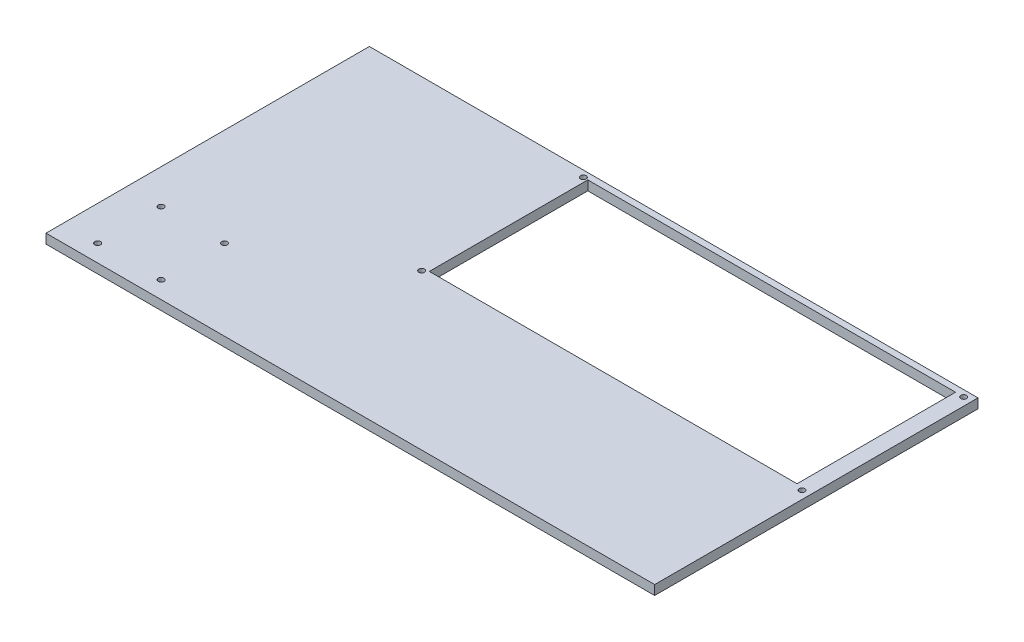
SolidWorks part; units mm, degrees
material "Balsa"
ref_plane "Front Plane" through (0, 0, 0) normal (0, 0, 1) x (1, 0, 0)
ref_plane "Top Plane" through (0, 0, 0) normal (0, 1, 0) x (1, 0, 0)
ref_plane "Right Plane" through (0, 0, 0) normal (1, 0, 0) x (0, 0, -1)
sketch "Sketch1" plane through (0, 0, 0) normal (0, 1, 0) x (1, 0, 0)
  line L1 (480, -255) -> (-480, -255)
  line L2 (480, -255) -> (480, 255)
  line L3 (480, 255) -> (-480, 255)
  line L4 (-480, -255) -> (-480, 255)
  line L5 (480, -255) -> (-480, 255) construction
  line L6 (480, 255) -> (-480, -255) construction
  point P0 (0, 0)
  dimension "D1" = 510
  dimension "D2" = 960
extrude "Boss-Extrude1" add sketch "Sketch1" along normal mid plane 15
sketch "Sketch3" plane through (0, 7.5, 0) normal (0, 1, 0) x (1, 0, 0)
  line L1 (454.5475, 245) -> (-125.4525, 245)
  line L2 (454.5475, 245) -> (454.5475, -5)
  line L3 (454.5475, -5) -> (-125.4525, -5)
  line L4 (-125.4525, 245) -> (-125.4525, -5)
  line L5 (480, -255) -> (480, 255) construction
  line L6 (480, 255) -> (-480, 255) construction
  point P4 (164.5475, -5)
  dimension "D1" = 250
  dimension "D2" = 580
  dimension "D3" = 25.4525
  dimension "D4" = 10
extrude "Cut-Extrude1" cut sketch "Sketch3" against normal through all
sketch "Esquisse2" [suppressed] plane through (0, 7.5, 0) normal (0, 1, 0) x (1, 0, 0)
  line L0 (480, 255) -> (-480, 255) construction
  line L1 (475, 255) -> (-85, 255)
  line L2 (475, 255) -> (475, 45)
  line L3 (475, 45) -> (-85, 45)
  line L4 (-85, 255) -> (-85, 45)
  line L5 (480, -255) -> (480, 255) construction
  dimension "D1" = 5
  dimension "D2" = 210
  dimension "D3" = 560
extrude "Enlèv. mat.-Extru.1" [suppressed] cut sketch "Esquisse2" against normal through all
sketch "Esquisse3" plane through (0, -7.5, 0) normal (0, -1, 0) x (1, 0, 0)
  line L1 (-425.5, 128) -> (-325.5, 128) construction
  line L2 (-425.5, 128) -> (-425.5, 228) construction
  line L3 (-425.5, 228) -> (-325.5, 228) construction
  line L4 (-325.5, 128) -> (-325.5, 228) construction
  line L5 (-132.5, 10) -> (467.5, 10) construction
  line L6 (-132.5, 10) -> (-132.5, -245) construction
  line L7 (-132.5, -245) -> (467.5, -245) construction
  line L8 (467.5, 10) -> (467.5, -245) construction
  line L9 (-480, 255) -> (480, 255) construction
  line L10 (-480, -255) -> (-480, 255) construction
  line L11 (480, -255) -> (-480, -255) construction
  line L12 (480, 255) -> (480, -255) construction
  circle A0 centre (-425.5, 228) radius 4.5
  circle A1 centre (-425.5, 128) radius 4.5
  circle A2 centre (-325.5, 128) radius 4.5
  circle A3 centre (-325.5, 228) radius 4.5
  circle A4 centre (-132.5, 10) radius 4.5
  circle A5 centre (-132.5, -245) radius 4.5
  circle A6 centre (467.5, -245) radius 4.5
  circle A7 centre (467.5, 10) radius 4.5
  dimension "D1" = 9
  dimension "D2" = 27
  dimension "D3" = 54.5
  dimension "D4" = 100
  dimension "D5" = 600
  dimension "D6" = 255
  dimension "D7" = 10
  dimension "D8" = 12.5
extrude "Enlèv. mat.-Extru.2" cut sketch "Esquisse3" against normal through all
